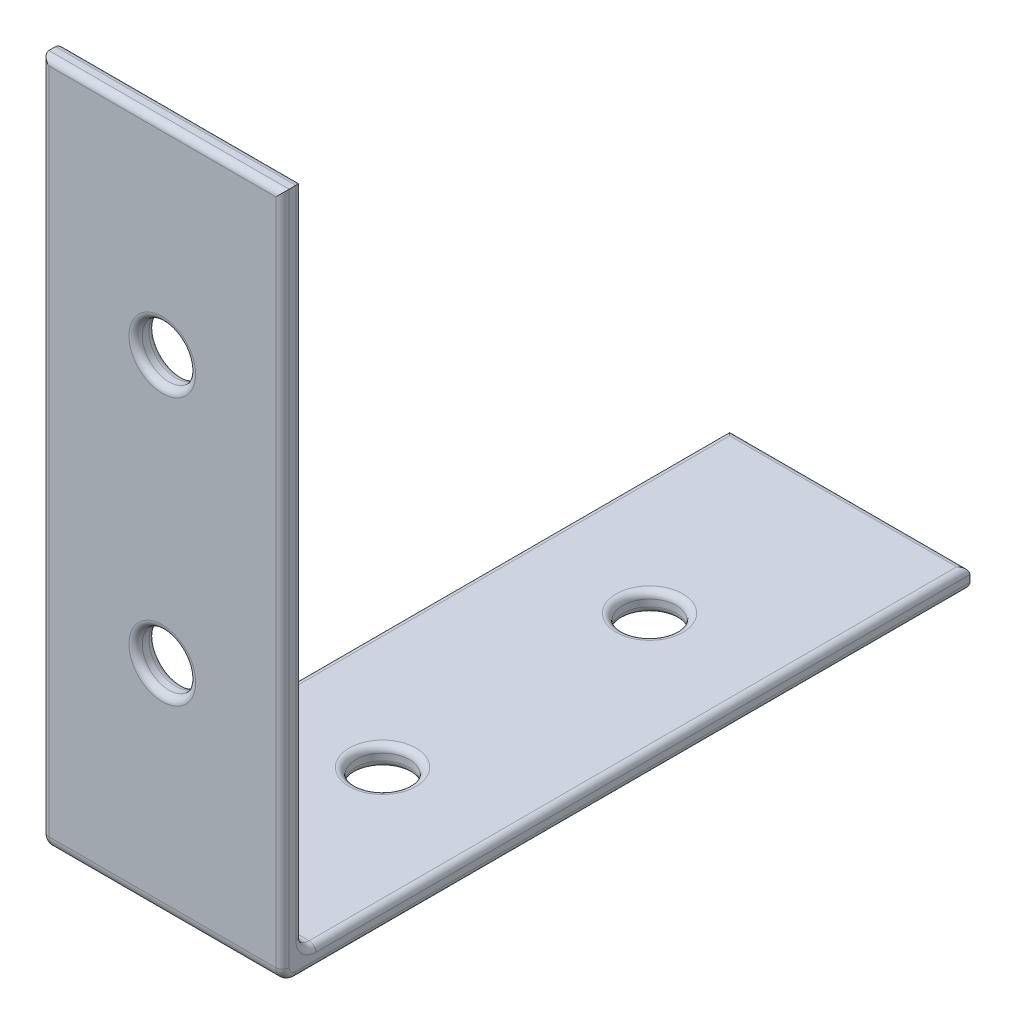
SolidWorks part; units mm, degrees
ref_plane "Front Plane" through (0, 0, 0) normal (0, 0, 1) x (1, 0, 0)
ref_plane "Top Plane" through (0, 0, 0) normal (0, 1, 0) x (1, 0, 0)
ref_plane "Right Plane" through (0, 0, 0) normal (1, 0, 0) x (0, 0, -1)
sketch "Sketch1" plane through (0, 0, 0) normal (1, 0, 0) x (0, 0, -1)
  line L1 (1, 0) -> (1.5, 0)
  line L2 (0, 1) -> (0, 51.5)
  line L3 (0, 51.5) -> (1.5, 51.5)
  line L4 (1.5, 2.5) -> (1.5, 51.5)
  line L5 (0, 0) -> (51.5, 0)
  line L6 (0, 0) -> (0, 1.5)
  line L7 (2.5, 1.5) -> (51.5, 1.5)
  line L8 (51.5, 0) -> (51.5, 1.5)
  arc A0 (2.5, 1.5) -> (1.5, 2.5) centre (2.5, 2.5) cw
  arc A1 (1, 0) -> (0, 1) centre (1, 1) cw
  dimension "D5" = 1
  dimension "D1" = 51.5
  dimension "D2" = 1.5
  dimension "D3" = 51.5
  dimension "D4" = 1.5
extrude "Boss-Extrude1" add sketch "Sketch1" along normal blind 18 contours A1 L1 L5 L8 L7 A0 L4 L3 L2
sketch "Sketch2" plane through (0, 1.5, 0) normal (0, 1, 0) x (1, 0, 0)
  line L0 (18, 1.5) -> (0, 1.5) construction
  circle A0 centre (9, 16.5) radius 2
  circle A1 centre (9, 36.5) radius 2
  point P6 (9, 1.5)
  dimension "D1" = 4
  dimension "D2" = 4
  dimension "D3" = 15
  dimension "D4" = 20
extrude "Cut-Extrude1" cut sketch "Sketch2" against normal through all
sketch "Sketch3" plane through (0, 0, -1.5) normal (0, 0, -1) x (-1, 0, 0)
  line L0 (-18, 1.5) -> (0, 1.5) construction
  circle A0 centre (-9, 16.5) radius 2
  circle A1 centre (-9, 36.5) radius 2
  point P6 (-9, 1.5)
  dimension "D1" = 4
  dimension "D2" = 4
  dimension "D3" = 15
  dimension "D4" = 20
extrude "Cut-Extrude2" cut sketch "Sketch3" against normal through all
fillet "Fillet1" radius 0.5 24 edges at (0, 0, -26.25) (0, 0.2929, -0.2929) (0, 1.5, -27) (0, 1.7929, -1.7929) (18, 27, -1.5) (18, 1.7929, -1.7929) (18, 26.25, 0) (18, 0.2929, -0.2929) (9, 51.5, -1.5) (9, 51.5, 0) (9, 0, -34.5) (9, 1.5, -34.5) (9, 1.5, -14.5) (9, 0, -14.5) (9, 18.5, 0) (9, 18.5, -1.5) (9, 38.5, 0) (9, 38.5, -1.5) (9, 0, -51.5) (9, 1.5, -51.5) (0, 26.25, 0) (0, 27, -1.5) (18, 1.5, -27) (18, 0, -26.25)
